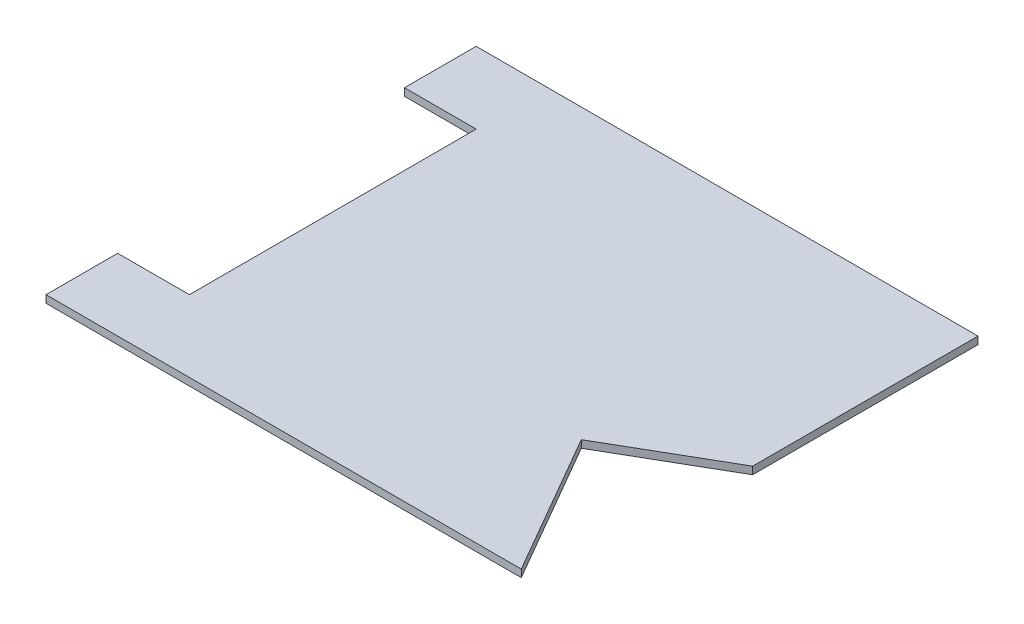
SolidWorks part; units mm, degrees
ref_plane "Front Plane" through (0, 0, 0) normal (0, 0, 1) x (1, 0, 0)
ref_plane "Top Plane" through (0, 0, 0) normal (0, 1, 0) x (1, 0, 0)
ref_plane "Right Plane" through (0, 0, 0) normal (1, 0, 0) x (0, 0, -1)
sketch "Sketch1" plane through (0, 0, 0) normal (0, 1, 0) x (1, 0, 0)
  line L0 (0, -762) -> (152.4, -762)
  line L1 (0, 0) -> (1066.8, 0)
  line L2 (0, 0) -> (0, -152.4)
  line L3 (0, -914.4) -> (1010.285, -914.4)
  line L4 (1066.8, 0) -> (1066.8, -479.0186)
  line L5 (0, -152.4) -> (152.4, -152.4)
  line L6 (152.4, -152.4) -> (152.4, -762)
  line L7 (0, -762) -> (0, -914.4)
  line L8 (1066.8, 0) -> (1066.8, -479.0186) construction
  line L9 (0, 0) -> (0, -914.4) construction
  line L10 (152.4, 0) -> (152.4, -914.4) construction
  line L11 (0, -762) -> (1066.8, -762) construction
  line L12 (0, -152.4) -> (1066.8, -152.4) construction
  line L13 (0, -914.4) -> (1010.285, -914.4) construction
  line L15 (0, -914.4) -> (959.485, -914.4) construction
  line L16 (1066.8, 0) -> (1066.8, -479.0186) construction
  line L19 (1010.285, -914.4) -> (835.8886, -612.3432)
  line L20 (835.8886, -612.3432) -> (1066.8, -479.0186)
  line L22 (0, -914.4) -> (1066.8, -914.4) construction
  dimension "D1" = 914.4
  dimension "D3" = 152.4
  dimension "D4" = 152.4
  dimension "D5" = 152.4
extrude "Boss-Extrude1" add sketch "Sketch1" along normal blind 15.875
